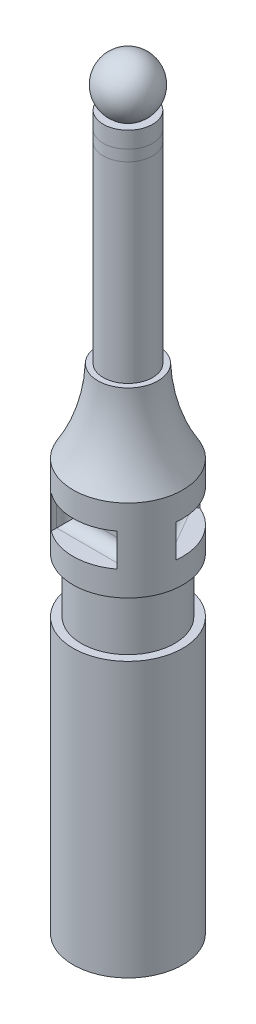
SolidWorks part; units mm, degrees
ref_plane "前视基准面" through (0, 0, 0) normal (0, 0, 1) x (1, 0, 0)
ref_plane "上视基准面" through (0, 0, 0) normal (0, 1, 0) x (1, 0, 0)
ref_plane "右视基准面" through (0, 0, 0) normal (1, 0, 0) x (0, 0, -1)
sketch "草图1" plane through (0, 0, 0) normal (0, 0, 1) x (1, 0, 0)
  line L0 (0, 64.0328) -> (0, -33.542) construction
  line L1 (-4.5, 96.458) -> (-3, 96.458)
  line L2 (-4.5, 96.458) -> (-4.5, 56.458)
  line L3 (-4.5, 56.458) -> (-5.5, 56.458)
  line L4 (-10, 41.458) -> (-10, 26.458)
  line L5 (-10, 16.458) -> (-8.5, 16.458)
  line L6 (-8.5, 16.458) -> (-8.5, 26.458)
  line L7 (-8.5, 26.458) -> (-10, 26.458)
  line L8 (-10, 16.458) -> (-10, -33.542)
  line L9 (-10, -33.542) -> (0, -33.542)
  line L10 (0, -33.542) -> (0, 105.458)
  arc A0 (0, 105.458) -> (-3, 96.458) centre (0, 100.458) ccw
  arc A1 (-5.5, 56.458) -> (-10, 41.458) centre (-36.2794, 57.5168) cw
  dimension "D1" = 5
  dimension "D2" = 4.5
  dimension "D3" = 40
  dimension "D4" = 15
  dimension "D5" = 15
  dimension "D6" = 10
  dimension "D7" = 50
  dimension "D8" = 10
  dimension "D9" = 1
  dimension "D10" = 1.5
  dimension "D11" = 9
revolve "旋转1" add sketch "草图1" angle 360 about L0
ref_plane "基准面1" through (0, 0, 24) normal (0, 0, 1) x (1, 0, 0)
sketch "草图3" plane through (0, 0, 24) normal (0, 0, 1) x (1, 0, 0)
  line L0 (0, 26.458) -> (0, 41.458) construction
  line L1 (-8.5, 26.458) -> (8.5, 26.458) construction
  line L2 (-10, 41.458) -> (10, 41.458) construction
  line L4 (-6, 36.958) -> (6, 36.958)
  line L5 (-6, 36.958) -> (-6, 30.958)
  line L6 (-6, 30.958) -> (6, 30.958)
  line L7 (6, 36.958) -> (6, 30.958)
  line L8 (-6, 36.958) -> (6, 30.958) construction
  line L9 (-6, 30.958) -> (6, 36.958) construction
  point P6 (0, 33.958)
  dimension "D1" = 12
  dimension "D2" = 6
extrude "切除-拉伸1" cut sketch "草图3" against normal blind 19
fillet "圆角1" radius 2 4 edges at (0, 30.958, 5) (6, 33.958, 5) (0, 36.958, 5) (-6, 33.958, 5)
pattern_circular "阵列(圆周)1" count 3 over 360 about axis through (0, 0, 0) along (0, 1, 0) of "圆角1", "切除-拉伸1"
ref_plane "基准面2" through (0, 93.458, 0) normal (0, 1, 0) x (1, 0, 0)
sketch "草图6" plane through (0, 93.458, 0) normal (0, 1, 0) x (1, 0, 0)
  circle A0 centre (0, 0) radius 4.5
  circle A1 centre (0, 0) radius 0.0005
  dimension "D1" = 0.001
extrude "切除-拉伸5" cut sketch "草图6" against normal blind 2
sketch "草图7" plane through (0, 93.458, 0) normal (0, 1, 0) x (1, 0, 0)
  circle A0 centre (0, 0) radius 4.5
extrude "凸台-拉伸3" add sketch "草图7" against normal blind 2 separate body
